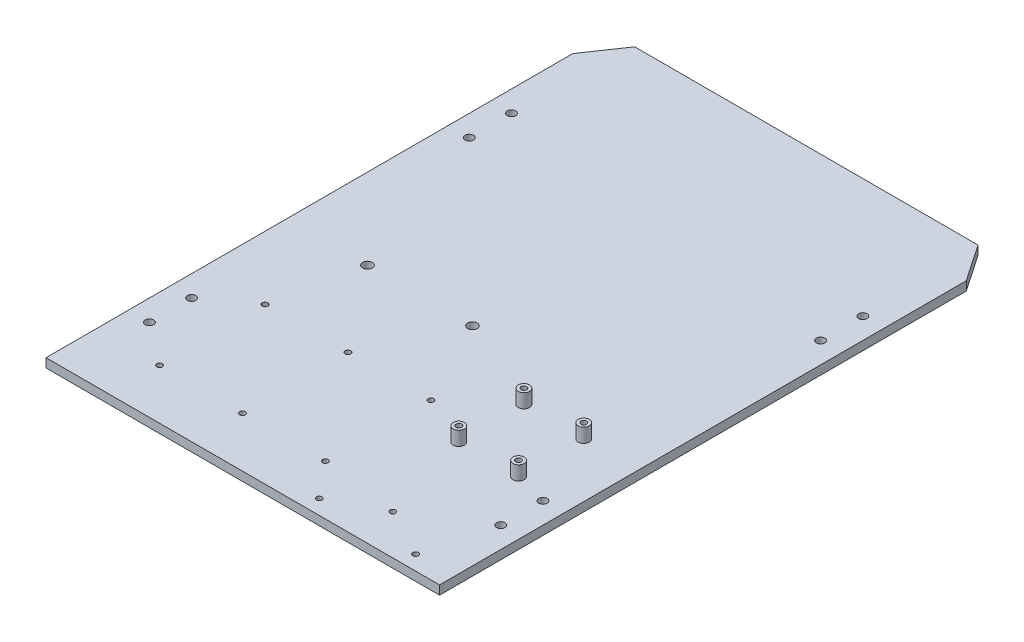
SolidWorks part; units mm, degrees
ref_plane "Front Plane" through (0, 0, 0) normal (0, 0, 1) x (1, 0, 0)
ref_plane "Top Plane" through (0, 0, 0) normal (0, 1, 0) x (1, 0, 0)
ref_plane "Right Plane" through (0, 0, 0) normal (1, 0, 0) x (0, 0, -1)
sketch "Sketch2" plane through (0, 0, 0) normal (0, 1, 0) x (1, 0, 0)
  line L0 (0, 0) -> (280, 0)
  line L1 (280, 0) -> (280, 374.8)
  line L2 (0, 0) -> (20, 0) construction
  line L3 (280, 374.8) -> (262.1427, 401.0063)
  line L4 (140, 401.01) -> (262.1427, 401.0063)
  line L5 (0, 374.8) -> (17.8573, 401.0063)
  line L6 (0, 0) -> (0, 374.8)
  line L7 (140, 401.01) -> (17.8573, 401.0063)
  line L8 (140, 401.01) -> (140, 323.2984) construction
  line L9 (0, 187.4) -> (71.7792, 187.4) construction
  circle A0 centre (45.126, 35.7096) radius 2
  circle A1 centre (45.126, 110.7096) radius 2
  circle A2 centre (104.126, 35.7096) radius 2
  circle A3 centre (104.126, 110.7096) radius 2
  circle A4 centre (163.126, 35.7096) radius 2
  circle A5 centre (163.126, 110.7096) radius 2
  circle A6 centre (57.3824, 171.3778) radius 3.455
  circle A7 centre (132.0324, 171.3778) radius 3.455
  circle A8 centre (252.5237, 10.5) radius 2
  circle A9 centre (218.2337, 28.5) radius 2
  circle A10 centre (183.9437, 10.5) radius 2
  circle A11 centre (265, 88.6055) radius 3
  circle A12 centre (265, 58.6055) radius 3
  circle A13 centre (15, 58.6055) radius 3
  circle A14 centre (15, 88.6055) radius 3
  circle A15 centre (265, 316.1945) radius 3
  circle A16 centre (265, 286.1945) radius 3
  circle A17 centre (15, 316.1945) radius 3
  circle A18 centre (15, 286.1945) radius 3
extrude "Boss-Extrude1" add sketch "Sketch2" along normal blind 6.35
sketch "Sketch3" plane through (0, 6.35, 0) normal (0, 1, 0) x (1, 0, 0)
  circle A2 centre (241.3216, 94.9327) radius 2
  circle A3 centre (241.3216, 141.2877) radius 2
  circle A4 centre (198.7766, 141.2877) radius 2
  circle A5 centre (198.7766, 94.9327) radius 2
  circle A6 centre (241.3216, 94.9327) radius 4
  circle A7 centre (198.7766, 94.9327) radius 4
  circle A8 centre (198.7766, 141.2877) radius 4
  circle A9 centre (241.3216, 141.2877) radius 4
extrude "Boss-Extrude2" add sketch "Sketch3" along normal blind 10
